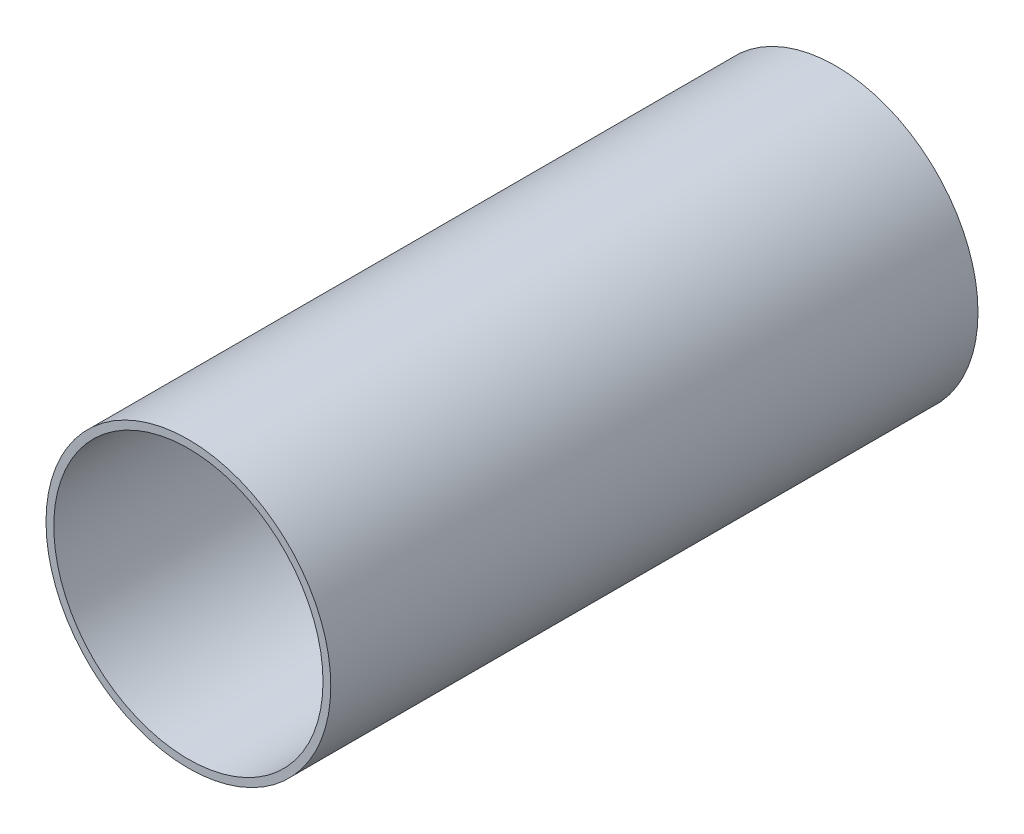
SolidWorks part; units mm, degrees
ref_plane "前视基准面" through (0, 0, 0) normal (0, 0, 1) x (1, 0, 0)
ref_plane "上视基准面" through (0, 0, 0) normal (0, 1, 0) x (1, 0, 0)
ref_plane "右视基准面" through (0, 0, 0) normal (1, 0, 0) x (0, 0, -1)
other "Configuration Table"
sketch "草图2" plane through (0, 0, 0) normal (0, 0, 1) x (1, 0, 0)
  circle A0 centre (0, 0) radius 55
  circle A1 centre (0, 0) radius 52
  dimension "D1" = 110
  dimension "D2" = 3
extrude "凸台-拉伸1" add sketch "草图2" along normal blind 250
